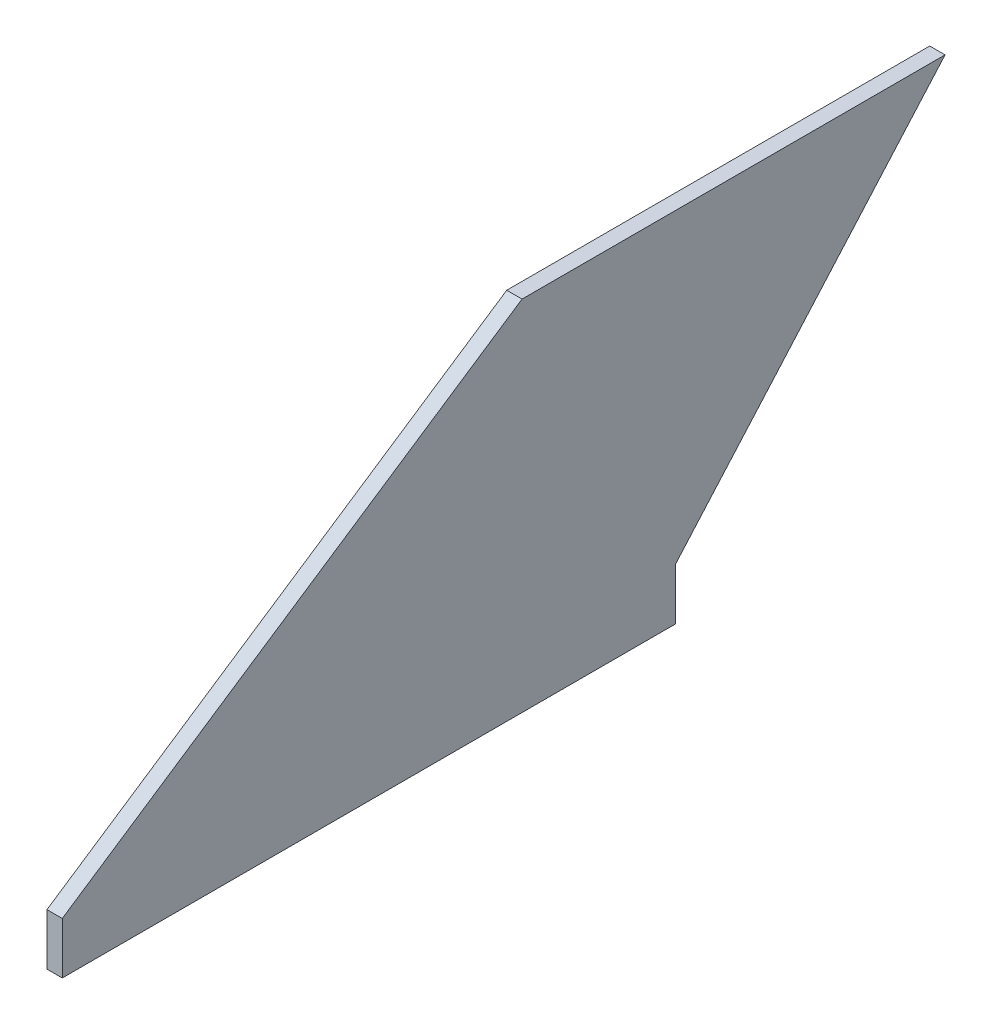
SolidWorks part; units mm, degrees
ref_plane "Front Plane" through (0, 0, 0) normal (0, 0, 1) x (1, 0, 0)
ref_plane "Top Plane" through (0, 0, 0) normal (0, 1, 0) x (1, 0, 0)
ref_plane "Right Plane" through (0, 0, 0) normal (1, 0, 0) x (0, 0, -1)
sketch "Sketch2" plane through (0, 0, 0) normal (1, 0, 0) x (0, 0, -1)
  line L0 (0, 0) -> (95.25, 63.5)
  line L1 (0, -10.6807) -> (127, -10.6807)
  line L2 (0, -10.6807) -> (0, 0)
  line L3 (0, 0) -> (127, 0) construction
  line L4 (127, -10.6807) -> (127, 0)
  line L5 (0, -10.6807) -> (127, 0) construction
  line L6 (0, 0) -> (127, -10.6807) construction
  line L7 (95.25, 63.5) -> (182.88, 63.5)
  line L8 (182.88, 63.5) -> (127, 0)
  point P0 (63.5, -5.3403)
  dimension "D1" = 95.25
  dimension "D2" = 63.5
  dimension "D3" = 182.88
  dimension "D4" = 127
  dimension "D5" = 10.6807
extrude "Boss-Extrude1" add sketch "Sketch2" along normal blind 3.175
equation "\"AIRFRAME_OD\"= 3.091in"
equation "\"AIRFRAME_ID\"= 3.00in"
equation "\"FLAT_T\"= 0.125in"
equation "\"COUPLER_OD\"= 2.998in"
equation "\"COUPLER_ID\"= 2.875in"
equation "\"NOSE_EXP_L\"= 3.5in"
equation "\"NOSE_SHOULDER_L\"= 5in"
equation "\"MAIN_L\"= 30in"
equation "\"RECO_COUP_L\"= 6in"
equation "\"RECO_SWITCH_L\"= 1.5in"
equation "\"RECO_ROD_X\"= 1.5in"
equation "\"DROGUE_L\"= 14in"
equation "\"ATS_FORE_COUP_L\"= 4in"
equation "\"ATS_AFT_COUP_L\"= 2.5in"
equation "\"ATS_ROD_X\"= 2in"
equation "\"LOWER_L\"= 16in"
equation "\"FIN_ROOT\"= 5in"
equation "\"FIN_X\"= 0.75in"
equation "\"FIN_N\"= 4"
equation "\"MOTOR_OD\"= 2.25in"
equation "\"MOTOR_ID\"= 2.126in"
equation "\"MOTOR_L\"= 8in"
equation "\"CR_AFT_X\"= 0.5in"
equation "\"CR_FORE_X\"= 6in"
equation "\"D1@Boss-Extrude1\"=\"FLAT_T\""
equation "\"D4@Sketch2\"=\"FIN_ROOT\""
equation "\"D5@Sketch2\"=(\"AIRFRAME_OD\"-\"MOTOR_OD\")*0.5"
